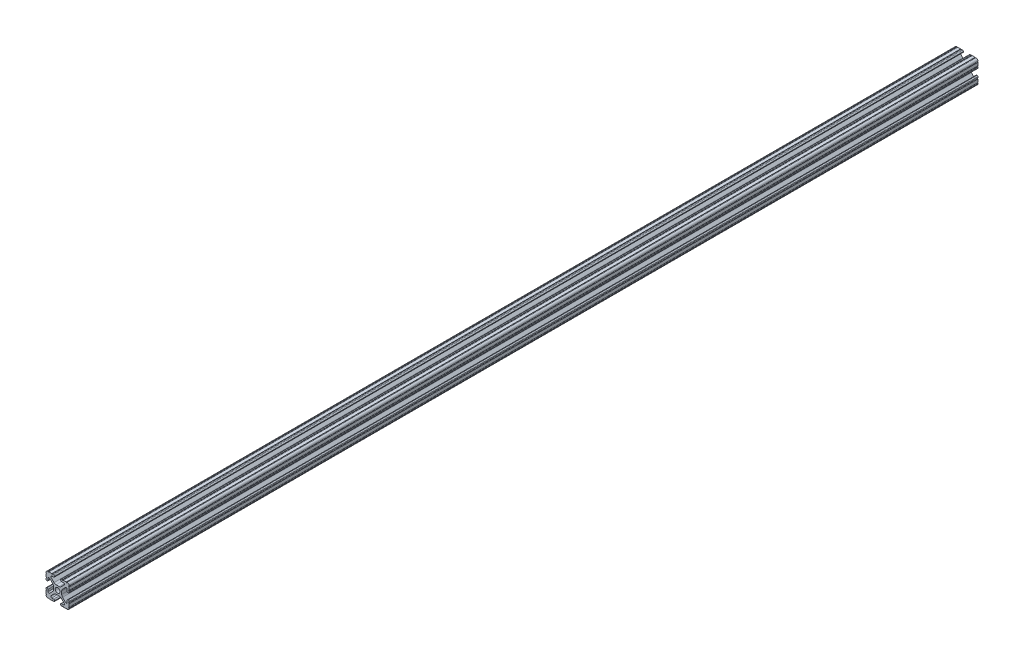
SolidWorks part; units mm, degrees
ref_plane "Front Plane" through (0, 0, 0) normal (0, 0, 1) x (1, 0, 0)
ref_plane "Top Plane" through (0, 0, 0) normal (0, 1, 0) x (1, 0, 0)
ref_plane "Right Plane" through (0, 0, 0) normal (1, 0, 0) x (0, 0, -1)
sketch "Sketch1" plane through (0, 0, 0) normal (0, 0, 1) x (1, 0, 0)
  line L88 (-7.1797, -8.6452) -> (-3.9523, -5.4237)
  line L89 (-1.7093, -4.4958) -> (1.7093, -4.4958)
  line L90 (3.9523, -5.4237) -> (7.1797, -8.6452)
  line L91 (6.4164, -10.4902) -> (4.2875, -10.4902)
  line L92 (3.2385, -11.5392) -> (3.2385, -11.651)
  line L93 (4.2875, -12.7) -> (5.3171, -12.7)
  line L94 (6.3331, -12.7) -> (9.5504, -12.7)
  line L95 (12.7, -9.5504) -> (12.7, -6.3331)
  line L96 (12.7, -5.3171) -> (12.7, -4.2875)
  line L97 (11.651, -3.2385) -> (11.5392, -3.2385)
  line L98 (10.4902, -4.2875) -> (10.4902, -6.4021)
  line L99 (8.7371, -7.1294) -> (5.441, -3.8408)
  line L100 (4.5085, -1.5932) -> (4.5085, 1.5932)
  line L101 (5.441, 3.8408) -> (8.7371, 7.1294)
  line L102 (10.4902, 6.4021) -> (10.4902, 4.2875)
  line L103 (11.5392, 3.2385) -> (11.651, 3.2385)
  line L104 (12.7, 4.2875) -> (12.7, 5.3171)
  line L105 (12.7, 6.3331) -> (12.7, 9.5504)
  line L106 (9.5504, 12.7) -> (6.3331, 12.7)
  line L107 (5.3171, 12.7) -> (4.2875, 12.7)
  line L108 (3.2385, 11.651) -> (3.2385, 11.5392)
  line L109 (4.2875, 10.4902) -> (6.4768, 10.4902)
  line L110 (7.207, 8.7244) -> (3.8983, 5.4232)
  line L111 (1.6558, 4.4958) -> (-1.6558, 4.4958)
  line L112 (-3.8983, 5.4232) -> (-7.207, 8.7244)
  line L113 (-6.4768, 10.4902) -> (-4.2875, 10.4902)
  line L114 (-3.2385, 11.5392) -> (-3.2385, 11.651)
  line L115 (-4.2875, 12.7) -> (-5.3171, 12.7)
  line L116 (-6.3331, 12.7) -> (-9.5504, 12.7)
  line L117 (-12.7, 9.5504) -> (-12.7, 6.3331)
  line L118 (-12.7, 5.3171) -> (-12.7, 4.2875)
  line L119 (-11.651, 3.2385) -> (-11.5392, 3.2385)
  line L120 (-10.4902, 4.2875) -> (-10.4902, 6.4021)
  line L121 (-8.7371, 7.1294) -> (-5.441, 3.8408)
  line L122 (-4.5085, 1.5932) -> (-4.5085, -1.5932)
  line L123 (-5.441, -3.8408) -> (-8.7371, -7.1294)
  line L124 (-10.4902, -6.4021) -> (-10.4902, -4.2875)
  line L125 (-11.5392, -3.2385) -> (-11.651, -3.2385)
  line L126 (-12.7, -4.2875) -> (-12.7, -5.3171)
  line L127 (-12.7, -6.3331) -> (-12.7, -9.5504)
  line L128 (-9.5504, -12.7) -> (-6.3331, -12.7)
  line L129 (-5.3171, -12.7) -> (-4.2875, -12.7)
  line L130 (-3.2385, -11.651) -> (-3.2385, -11.5392)
  line L131 (-4.2875, -10.4902) -> (-6.4164, -10.4902)
  circle A1 centre (0, 0) radius 2.6035
  arc A104 (-7.1797, -8.6452) -> (-6.4164, -10.4902) centre (-6.4164, -9.4098) ccw
  arc A105 (-1.7093, -4.4958) -> (-3.9523, -5.4237) centre (-1.7093, -7.6708) ccw
  arc A106 (3.9523, -5.4237) -> (1.7093, -4.4958) centre (1.7093, -7.6708) ccw
  arc A107 (6.4164, -10.4902) -> (7.1797, -8.6452) centre (6.4164, -9.4098) ccw
  arc A108 (4.2875, -10.4902) -> (3.2385, -11.5392) centre (4.2875, -11.5392) ccw
  arc A109 (3.2385, -11.651) -> (4.2875, -12.7) centre (4.2875, -11.651) ccw
  arc A110 (6.3331, -12.7) -> (5.3171, -12.7) centre (5.8251, -12.7) ccw
  arc A111 (10.5664, -12.6998) -> (9.5504, -12.7) centre (10.0584, -12.7) ccw
  arc A112 (10.5664, -12.6998) -> (12.6998, -10.5664) centre (10.5918, -10.5918) ccw
  arc A113 (12.7, -9.5504) -> (12.6998, -10.5664) centre (12.7, -10.0584) ccw
  arc A114 (12.7, -5.3171) -> (12.7, -6.3331) centre (12.7, -5.8251) ccw
  arc A115 (12.7, -4.2875) -> (11.651, -3.2385) centre (11.651, -4.2875) ccw
  arc A116 (11.5392, -3.2385) -> (10.4902, -4.2875) centre (11.5392, -4.2875) ccw
  arc A117 (8.7371, -7.1294) -> (10.4902, -6.4021) centre (9.4628, -6.4021) ccw
  arc A118 (4.5085, -1.5932) -> (5.441, -3.8408) centre (7.6835, -1.5932) ccw
  arc A119 (5.441, 3.8408) -> (4.5085, 1.5932) centre (7.6835, 1.5932) ccw
  arc A120 (10.4902, 6.4021) -> (8.7371, 7.1294) centre (9.4628, 6.4021) ccw
  arc A121 (10.4902, 4.2875) -> (11.5392, 3.2385) centre (11.5392, 4.2875) ccw
  arc A122 (11.651, 3.2385) -> (12.7, 4.2875) centre (11.651, 4.2875) ccw
  arc A123 (12.7, 6.3331) -> (12.7, 5.3171) centre (12.7, 5.8251) ccw
  arc A124 (12.6998, 10.5664) -> (12.7, 9.5504) centre (12.7, 10.0584) ccw
  arc A125 (12.6998, 10.5664) -> (10.5664, 12.6998) centre (10.5918, 10.5918) ccw
  arc A126 (9.5504, 12.7) -> (10.5664, 12.6998) centre (10.0584, 12.7) ccw
  arc A127 (5.3171, 12.7) -> (6.3331, 12.7) centre (5.8251, 12.7) ccw
  arc A128 (4.2875, 12.7) -> (3.2385, 11.651) centre (4.2875, 11.651) ccw
  arc A129 (3.2385, 11.5392) -> (4.2875, 10.4902) centre (4.2875, 11.5392) ccw
  arc A130 (7.207, 8.7244) -> (6.4768, 10.4902) centre (6.4768, 9.4563) ccw
  arc A131 (1.6558, 4.4958) -> (3.8983, 5.4232) centre (1.6558, 7.6708) ccw
  arc A132 (-3.8983, 5.4232) -> (-1.6558, 4.4958) centre (-1.6558, 7.6708) ccw
  arc A133 (-6.4768, 10.4902) -> (-7.207, 8.7244) centre (-6.4768, 9.4563) ccw
  arc A134 (-4.2875, 10.4902) -> (-3.2385, 11.5392) centre (-4.2875, 11.5392) ccw
  arc A135 (-3.2385, 11.651) -> (-4.2875, 12.7) centre (-4.2875, 11.651) ccw
  arc A136 (-6.3331, 12.7) -> (-5.3171, 12.7) centre (-5.8251, 12.7) ccw
  arc A137 (-10.5664, 12.6998) -> (-9.5504, 12.7) centre (-10.0584, 12.7) ccw
  arc A138 (-10.5664, 12.6998) -> (-12.6998, 10.5664) centre (-10.5918, 10.5918) ccw
  arc A139 (-12.7, 9.5504) -> (-12.6998, 10.5664) centre (-12.7, 10.0584) ccw
  arc A140 (-12.7, 5.3171) -> (-12.7, 6.3331) centre (-12.7, 5.8251) ccw
  arc A141 (-12.7, 4.2875) -> (-11.651, 3.2385) centre (-11.651, 4.2875) ccw
  arc A142 (-11.5392, 3.2385) -> (-10.4902, 4.2875) centre (-11.5392, 4.2875) ccw
  arc A143 (-8.7371, 7.1294) -> (-10.4902, 6.4021) centre (-9.4628, 6.4021) ccw
  arc A144 (-4.5085, 1.5932) -> (-5.441, 3.8408) centre (-7.6835, 1.5932) ccw
  arc A145 (-5.441, -3.8408) -> (-4.5085, -1.5932) centre (-7.6835, -1.5932) ccw
  arc A146 (-10.4902, -6.4021) -> (-8.7371, -7.1294) centre (-9.4628, -6.4021) ccw
  arc A147 (-10.4902, -4.2875) -> (-11.5392, -3.2385) centre (-11.5392, -4.2875) ccw
  arc A148 (-11.651, -3.2385) -> (-12.7, -4.2875) centre (-11.651, -4.2875) ccw
  arc A149 (-12.7, -6.3331) -> (-12.7, -5.3171) centre (-12.7, -5.8251) ccw
  arc A150 (-12.6998, -10.5664) -> (-12.7, -9.5504) centre (-12.7, -10.0584) ccw
  arc A151 (-12.6998, -10.5664) -> (-10.5664, -12.6998) centre (-10.5918, -10.5918) ccw
  arc A152 (-9.5504, -12.7) -> (-10.5664, -12.6998) centre (-10.0584, -12.7) ccw
  arc A153 (-5.3171, -12.7) -> (-6.3331, -12.7) centre (-5.8251, -12.7) ccw
  arc A154 (-4.2875, -12.7) -> (-3.2385, -11.651) centre (-4.2875, -11.651) ccw
  arc A155 (-3.2385, -11.5392) -> (-4.2875, -10.4902) centre (-4.2875, -11.5392) ccw
extrude "Boss-Extrude1" add sketch "Sketch1" along normal mid plane 995.8
